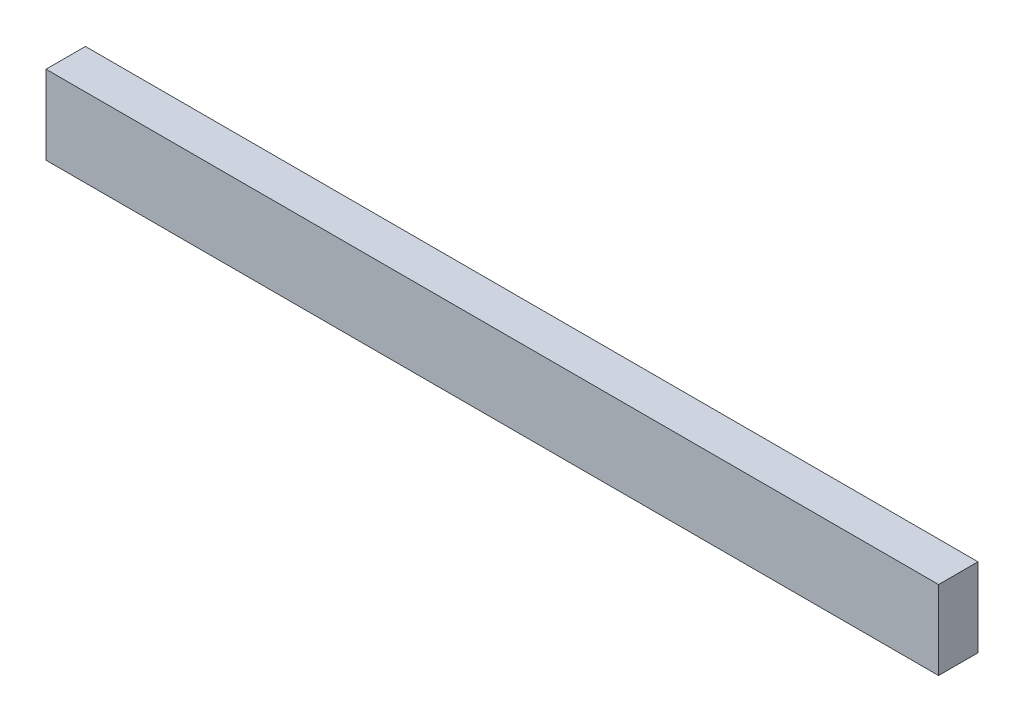
SolidWorks part; units mm, degrees
material "Cedar"
ref_plane "Front Plane" through (0, 0, 0) normal (0, 0, 1) x (1, 0, 0)
ref_plane "Top Plane" through (0, 0, 0) normal (0, 1, 0) x (1, 0, 0)
ref_plane "Right Plane" through (0, 0, 0) normal (1, 0, 0) x (0, 0, -1)
sketch "Sketch1" plane through (0, 0, 0) normal (0, 0, 1) x (1, 0, 0)
  line L1 (-174.2398, 30.7218) -> (257.103, 30.7218)
  line L2 (-174.2398, 30.7218) -> (-174.2398, -7.3782)
  line L3 (-174.2398, -7.3782) -> (257.103, -7.3782)
  line L4 (257.103, 30.7218) -> (257.103, -7.3782)
  dimension "D1" = 431.3428
  dimension "D2" = 38.1
extrude "Boss-Extrude1" add sketch "Sketch1" along normal blind 19.05
